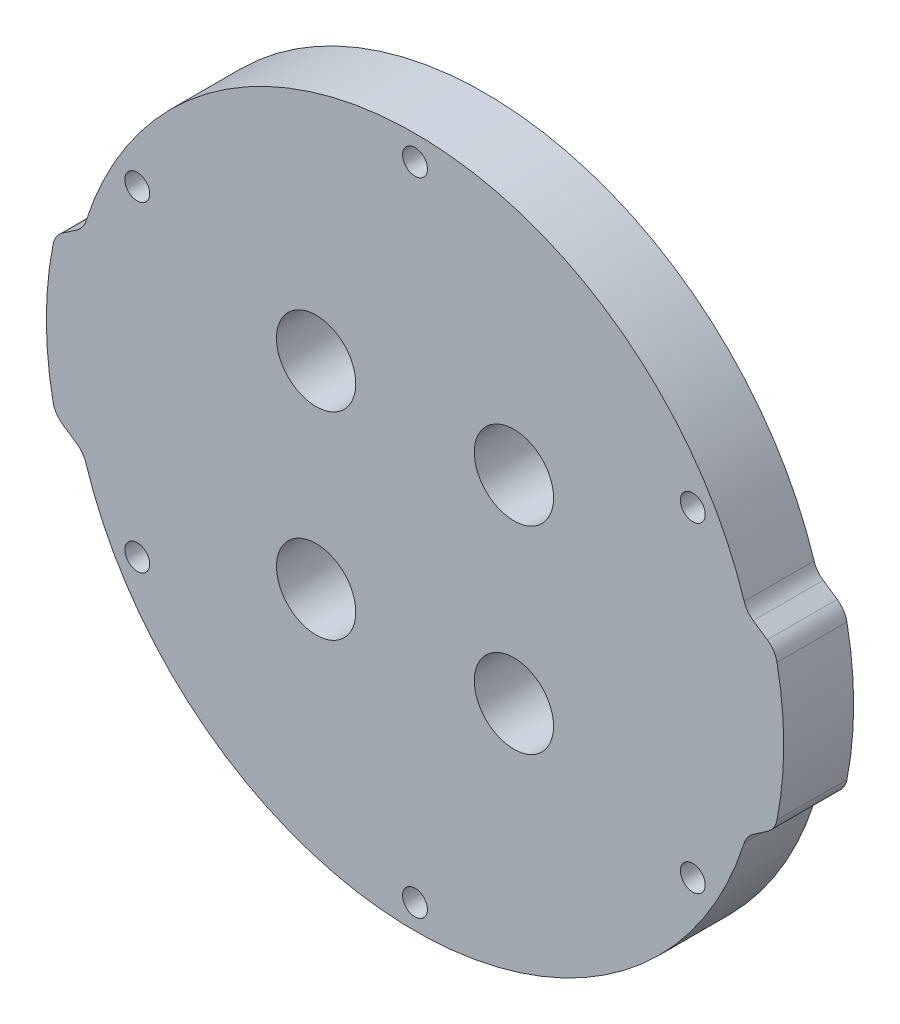
SolidWorks part; units mm, degrees
material "ABS PC"
ref_plane "Front Plane" through (0, 0, 0) normal (0, 0, 1) x (1, 0, 0)
ref_plane "Top Plane" through (0, 0, 0) normal (0, 1, 0) x (1, 0, 0)
ref_plane "Right Plane" through (0, 0, 0) normal (1, 0, 0) x (0, 0, -1)
sketch "Sketch1" plane through (0, 0, 0) normal (0, 0, 1) x (1, 0, 0)
  line L0 (-46.3248, 10) -> (-42.6562, 12.5)
  line L1 (-46.3248, -10) -> (-42.6562, -12.5)
  line L2 (46.3248, 10) -> (42.6562, 12.5)
  line L3 (46.3248, -10) -> (42.6562, -12.5)
  line L4 (0, 0) -> (35.7452, 20.6375) construction
  line L5 (35.7452, 20.6375) -> (38.4948, 22.225) construction
  line L6 (0, 41.275) -> (0, 0) construction
  line L7 (-47.5, 0) -> (0, 0) construction
  line L8 (0, 0) -> (47.5, 0) construction
  arc A0 (-42.6562, -12.5) -> (42.6562, -12.5) centre (0, 0) ccw
  circle A1 centre (0, 41.275) radius 1.6
  circle A2 centre (35.7452, 20.6375) radius 1.6
  circle A3 centre (35.7452, -20.6375) radius 1.6
  circle A4 centre (0, -41.275) radius 1.6
  circle A5 centre (-35.7452, -20.6375) radius 1.6
  circle A6 centre (-35.7452, 20.6375) radius 1.6
  arc A7 (-46.3248, 10) -> (-46.3248, -10) centre (-2.45, 0) ccw
  arc A8 (46.3248, 10) -> (46.3248, -10) centre (2.45, 0) cw
  arc A9 (42.6562, 12.5) -> (-42.6562, 12.5) centre (0, 0) ccw
  circle A10 centre (-47.5, 0) radius 1.6 construction
  circle A11 centre (-47.5, 0) radius 2.5 construction
  arc A12 (-42.6562, 12.5) -> (-42.6562, -12.5) centre (0, 0) ccw construction
  circle A13 centre (47.5, 0) radius 1.6 construction
  point P17 (0, 0)
  point P19 (-47.45, 0)
  dimension "D1" = 88.9
  dimension "D2" = 3.175
  dimension "D3" = 3.2
  dimension "D6" = 3
  dimension "D11" = 3.2
  dimension "D12" = 5
  dimension "D14" = 45
  dimension "D5" = 25
  dimension "D7" = 20
  dimension "D9" = 3.175
  dimension "D10" = 60
  dimension "D13" = 47.5
  dimension "D4" = 6
extrude "Boss-Extrude1" add sketch "Sketch1" along normal blind 9
fillet "Fillet1" radius 3 8 edges at (42.6562, 12.5, 4.5) (42.6562, -12.5, 4.5) (-42.6562, -12.5, 4.5) (-46.3248, -10, 4.5) (-42.6562, 12.5, 4.5) (-46.3248, 10, 4.5) (46.3248, -10, 4.5) (46.3248, 10, 4.5)
sketch "Sketch2" plane through (0, 0, 9) normal (0, 0, 1) x (1, 0, 0)
  line L0 (0, 0) -> (12.7279, 12.7279) construction
  line L1 (0, 0) -> (0, 31.75) construction
  circle A0 centre (0, 0) radius 31.75 construction
  circle A1 centre (12.7279, 12.7279) radius 5.1
  circle A2 centre (12.7279, 12.7279) radius 9 construction
  circle A3 centre (12.7279, -12.7279) radius 9 construction
  circle A4 centre (12.7279, -12.7279) radius 5.1
  circle A5 centre (-12.7279, -12.7279) radius 9 construction
  circle A6 centre (-12.7279, -12.7279) radius 5.1
  circle A7 centre (-12.7279, 12.7279) radius 9 construction
  circle A8 centre (-12.7279, 12.7279) radius 5.1
  point P19 (0, 0)
  point P23 (0, 0)
  dimension "D1" = 63.5
  dimension "D2" = 10.2
  dimension "D3" = 18
  dimension "D5" = 18
  dimension "D4" = 45
  dimension "D6" = 4
extrude "Cut-Extrude1" cut sketch "Sketch2" against normal through all
